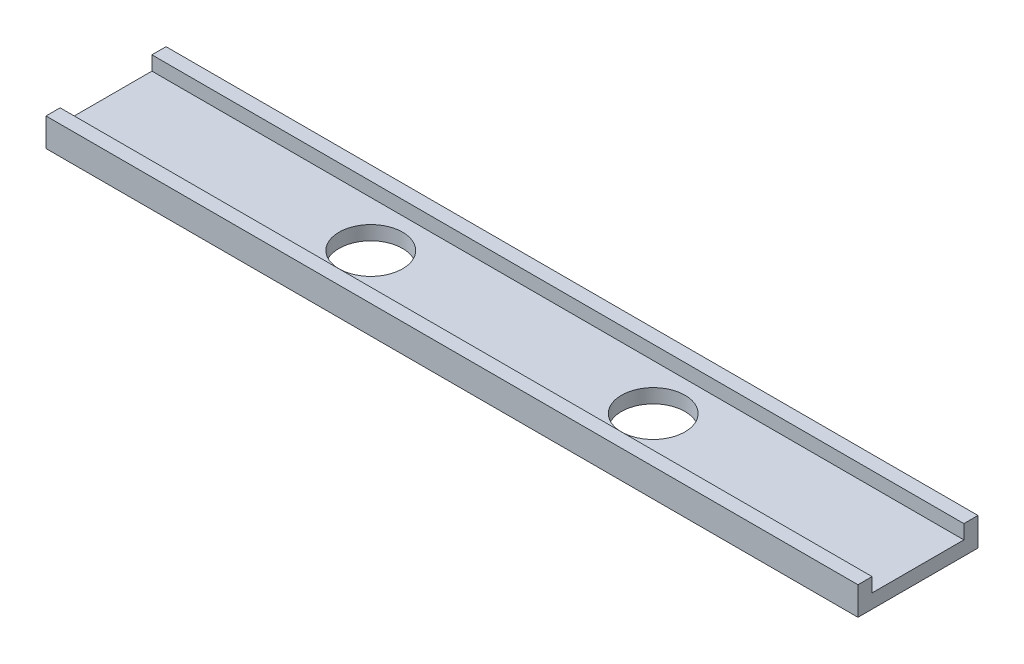
SolidWorks part; units mm, degrees
ref_plane "Plane1" through (0, 0, 0) normal (0, 0, 1) x (1, 0, 0)
ref_plane "Plane2" through (0, 0, 0) normal (0, 1, 0) x (1, 0, 0)
ref_plane "Plane3" through (0, 0, 0) normal (1, 0, 0) x (0, 0, -1)
sketch "Sketch1" plane through (0, 0, 0) normal (0, 0, 1) x (1, 0, 0)
  line L0 (-224.5988, -3.8279) -> (-218.4166, 1.3596) construction
  line L1 (-210.7031, 4.1671) -> (-188.0977, 4.1671) construction
  line L2 (-183.9934, 3.4434) -> (-177.3495, 1.0252) construction
  line L3 (-171.5352, 0) -> (-58.4648, 0) construction
  line L4 (-52.6505, 1.0252) -> (-46.0066, 3.4434) construction
  line L5 (-41.9023, 4.1671) -> (-19.2969, 4.1671) construction
  line L6 (-11.5834, 1.3596) -> (-5.4012, -3.8279) construction
  line L7 (-225.3649, -4.4706) -> (-218.4166, 1.3596)
  line L8 (-210.7031, 4.1671) -> (-188.0977, 4.1671)
  line L9 (-183.9934, 3.4434) -> (-177.3495, 1.0252)
  line L10 (-171.5352, 0) -> (-58.4648, 0)
  line L11 (-52.6505, 1.0252) -> (-46.0066, 3.4434)
  line L12 (-41.9023, 4.1671) -> (-19.2969, 4.1671)
  line L13 (-11.5834, 1.3596) -> (-4.6351, -4.4706)
  line L14 (-1.4212, -0.6404) -> (-4.6351, -4.4706) construction
  line L15 (-228.5788, -0.6404) -> (-225.3649, -4.4706) construction
  arc A0 (-210.7031, 4.1671) -> (-218.4166, 1.3596) centre (-210.7031, -7.8329) ccw construction
  arc A1 (-183.9934, 3.4434) -> (-188.0977, 4.1671) centre (-188.0977, -7.8329) ccw construction
  arc A2 (-177.3495, 1.0252) -> (-171.5352, 0) centre (-171.5352, 17) ccw construction
  arc A3 (-58.4648, 0) -> (-52.6505, 1.0252) centre (-58.4648, 17) ccw construction
  arc A4 (-41.9023, 4.1671) -> (-46.0066, 3.4434) centre (-41.9023, -7.8329) ccw construction
  arc A5 (-11.5834, 1.3596) -> (-19.2969, 4.1671) centre (-19.2969, -7.8329) ccw construction
  arc A6 (-210.7031, 4.1671) -> (-218.4166, 1.3596) centre (-210.7031, -7.8329) ccw
  arc A7 (-183.9934, 3.4434) -> (-188.0977, 4.1671) centre (-188.0977, -7.8329) ccw
  arc A8 (-177.3495, 1.0252) -> (-171.5352, 0) centre (-171.5352, 17) ccw
  arc A9 (-58.4648, 0) -> (-52.6505, 1.0252) centre (-58.4648, 17) ccw
  arc A10 (-41.9023, 4.1671) -> (-46.0066, 3.4434) centre (-41.9023, -7.8329) ccw
  arc A11 (-11.5834, 1.3596) -> (-19.2969, 4.1671) centre (-19.2969, -7.8329) ccw
ref_plane "Plane4" through (-4.6351, -4.4706, 0) normal (0.766, -0.6428, 0) x (0, 0, -1)
sketch "Sketch2" plane through (-4.6351, -4.4706, 0) normal (0.766, -0.6428, 0) x (0, 0, -1)
  line L0 (0, 0) -> (0.5, 0)
  line L1 (0.5, 0) -> (0.5, 4)
  line L2 (0.5, 4) -> (4.5, 4)
  line L3 (4.5, 4) -> (4.5, -4)
  line L4 (4.5, -4) -> (-29.5, -4)
  line L5 (-29.5, -4) -> (-29.5, 4)
  line L6 (-29.5, 4) -> (-25.5, 4)
  line L7 (-25.5, 4) -> (-25.5, 0)
  line L8 (-25.5, 0) -> (0, 0)
  line L10 (-12.5, 5) -> (-12.5, -4) construction
  line L11 (-24, 5) -> (-1, 5) construction
  dimension "D1" = 26
  dimension "D2" = 4
  dimension "D3" = 4
  dimension "D4" = 8
sweep "Sweep1" add profiles "Sketch2" path "Sketch1"
ref_plane "Symmetriplan" through (-115, 4, 29.5) normal (-1, 0, 0) x (0, 0, 1)
ref_plane "Plane6" through (-230, 0, 0) normal (-1, 0, 0) x (0, 0, 1)
sketch "Sketch5" plane through (0, -4, 0) normal (0, -1, 0) x (1, 0, 0)
  line L0 (-115, 29.5) -> (-115, -4.5) construction
  line L1 (-58.4648, 29.5) -> (-171.5352, 29.5) construction
  line L2 (-58.4648, -4.5) -> (-171.5352, -4.5) construction
  line L3 (-115, 12.5) -> (-75, 12.5) construction
  circle A0 centre (-75, 12.5) radius 9
  circle A1 centre (-155, 12.5) radius 9
  dimension "D2" = 18
  dimension "D1" = 80
extrude "2 stk ø18 huller" cut sketch "Sketch5" against normal through all
sketch "Sketch3" plane through (0, 0, 29.5) normal (0, 0, 1) x (1, 0, 0)
  line L0 (-115, -4) -> (-115, 36.4822) construction
  line L1 (-65, 18.1671) -> (-2.064, 18.1671)
  line L2 (-65, 18.1671) -> (-65, -14)
  line L3 (-65, -14) -> (-2.064, -14)
  line L4 (-2.064, 18.1671) -> (-2.064, -14)
  line L5 (-58.4648, -4) -> (-171.5352, -4) construction
  line L6 (-19.2969, 8.1671) -> (-41.9023, 8.1671) construction
  line L7 (-227.936, 18.1671) -> (-227.936, -14) construction
  line L8 (-165, -14) -> (-227.936, -14) construction
  line L9 (-165, 18.1671) -> (-165, -14) construction
  line L10 (-165, 18.1671) -> (-227.936, 18.1671) construction
  dimension "D1" = 10
  dimension "D2" = 10
  dimension "D3" = 50
extrude "Dummy cut away1" cut sketch "Sketch3" against normal through all
sketch "Sketch6" plane through (0, 0, 29.5) normal (0, 0, 1) x (1, 0, 0)
  line L0 (-165, 18.1671) -> (-227.936, 18.1671) construction
  line L1 (-227.936, 18.1671) -> (-227.936, -14) construction
  line L2 (-165, -14) -> (-227.936, -14) construction
  line L3 (-165, 18.1671) -> (-165, -14) construction
  line L4 (-165, 18.1671) -> (-227.936, 18.1671)
  line L5 (-227.936, 18.1671) -> (-227.936, -14)
  line L6 (-165, -14) -> (-227.936, -14)
  line L7 (-165, 18.1671) -> (-165, -14)
extrude "Dummy cut away2" cut sketch "Sketch6" against normal through all
sketch "Sketch4" plane through (-165, 0, 0) normal (-1, 0, 0) x (0, 0, 1)
  line L8 (29.5, -4) -> (29.5, 4)
  line L9 (29.5, 4) -> (25.5, 4)
  line L10 (25.5, 4) -> (25.5, 0)
  line L11 (25.5, 0) -> (-0.5, 0)
  line L12 (-0.5, 0) -> (-0.5, 4)
  line L13 (-0.5, 4) -> (-4.5, 4)
  line L14 (-4.5, 4) -> (-4.5, -4)
  line L15 (-4.5, -4) -> (29.5, -4)
  line L16 (29.5, -4) -> (29.5, 4)
  line L17 (29.5, 4) -> (25.5, 4)
  line L18 (25.5, 4) -> (25.5, 0)
  line L19 (25.5, 0) -> (-0.5, 0)
  line L20 (-0.5, 0) -> (-0.5, 4)
  line L21 (-0.5, 4) -> (-4.5, 4)
  line L22 (-4.5, 4) -> (-4.5, -4)
  line L23 (-4.5, -4) -> (29.5, -4)
  dimension "D1" = 0
extrude "Dummy ret1" add sketch "Sketch4" along normal blind 65
mirror "Mirror1" about plane through (-115, 4, 29.5) normal (-1, 0, 0) of "Dummy ret1"
sketch "Sketch8" [suppressed] plane through (0, 0, 29.5) normal (0, 0, 1) x (1, 0, 0)
  line L0 (-165, 0) -> (-200.8841, 0)
  line L1 (-204.9883, 0.7237) -> (-212.0016, 3.2763)
  line L2 (-220.2101, 3.2763) -> (-228, 0.441)
  line L3 (-165, -4) -> (-165, 4) construction
  arc A0 (-212.0016, 3.2763) -> (-220.2101, 3.2763) centre (-216.1058, -8) ccw
  arc A1 (-200.8841, 0) -> (-204.9883, 0.7237) centre (-200.8841, 12) cw
  point P13 (-203, 0)
  dimension "D4" = 12
  dimension "D6" = 8
  dimension "D1" = 20
  dimension "D2" = 40
  dimension "D3" = 38
  dimension "D5" = 25
sketch "Sketch9" [suppressed] plane through (-165, 0, 0) normal (-1, 0, 0) x (0, 0, 1)
  line L8 (29.5, -4) -> (29.5, 4)
  line L9 (29.5, 4) -> (25.5, 4)
  line L10 (25.5, 4) -> (25.5, 0)
  line L11 (25.5, 0) -> (-0.5, 0)
  line L12 (-0.5, 0) -> (-0.5, 4)
  line L13 (-0.5, 4) -> (-4.5, 4)
  line L14 (-4.5, 4) -> (-4.5, -4)
  line L15 (-4.5, -4) -> (29.5, -4)
  line L16 (29.5, -4) -> (29.5, 4)
  line L17 (29.5, 4) -> (25.5, 4)
  line L18 (25.5, 4) -> (25.5, 0)
  line L19 (25.5, 0) -> (-0.5, 0)
  line L20 (-0.5, 0) -> (-0.5, 4)
  line L21 (-0.5, 4) -> (-4.5, 4)
  line L22 (-4.5, 4) -> (-4.5, -4)
  line L23 (-4.5, -4) -> (29.5, -4)
  dimension "D1" = 0
sweep "Dummy ende - 1stk 1/2\"" [suppressed] add profiles "Sketch9" path "Sketch8"
sketch "Sketch10" [suppressed] plane through (0, 0, 29.5) normal (0, 0, 1) x (1, 0, 0)
  line L0 (-65, 0) -> (-18.8676, 0)
  line L1 (-11.1542, -2.8075) -> (-4.25, -8.6008)
  arc A0 (-18.8676, 0) -> (-11.1542, -2.8075) centre (-18.8676, -12) cw
  point P7 (-14.5, 0)
  dimension "D2" = 12
  dimension "D1" = 40
  dimension "D3" = 50.5
  dimension "D4" = 10.25
sketch "Sketch11" [suppressed] plane through (-65, 0, 0) normal (1, 0, 0) x (0, 0, -1)
  line L8 (4.5, -4) -> (4.5, 4)
  line L9 (4.5, 4) -> (0.5, 4)
  line L10 (0.5, 4) -> (0.5, 0)
  line L11 (0.5, 0) -> (-25.5, 0)
  line L12 (-25.5, 0) -> (-25.5, 4)
  line L13 (-25.5, 4) -> (-29.5, 4)
  line L14 (-29.5, 4) -> (-29.5, -4)
  line L15 (-29.5, -4) -> (4.5, -4)
  line L16 (4.5, -4) -> (4.5, 4)
  line L17 (4.5, 4) -> (0.5, 4)
  line L18 (0.5, 4) -> (0.5, 0)
  line L19 (0.5, 0) -> (-25.5, 0)
  line L20 (-25.5, 0) -> (-25.5, 4)
  line L21 (-25.5, 4) -> (-29.5, 4)
  line L22 (-29.5, 4) -> (-29.5, -4)
  line L23 (-29.5, -4) -> (4.5, -4)
  dimension "D1" = 0
sweep "Dummy ende - opbuk" [suppressed] add profiles "Sketch11" path "Sketch10"
